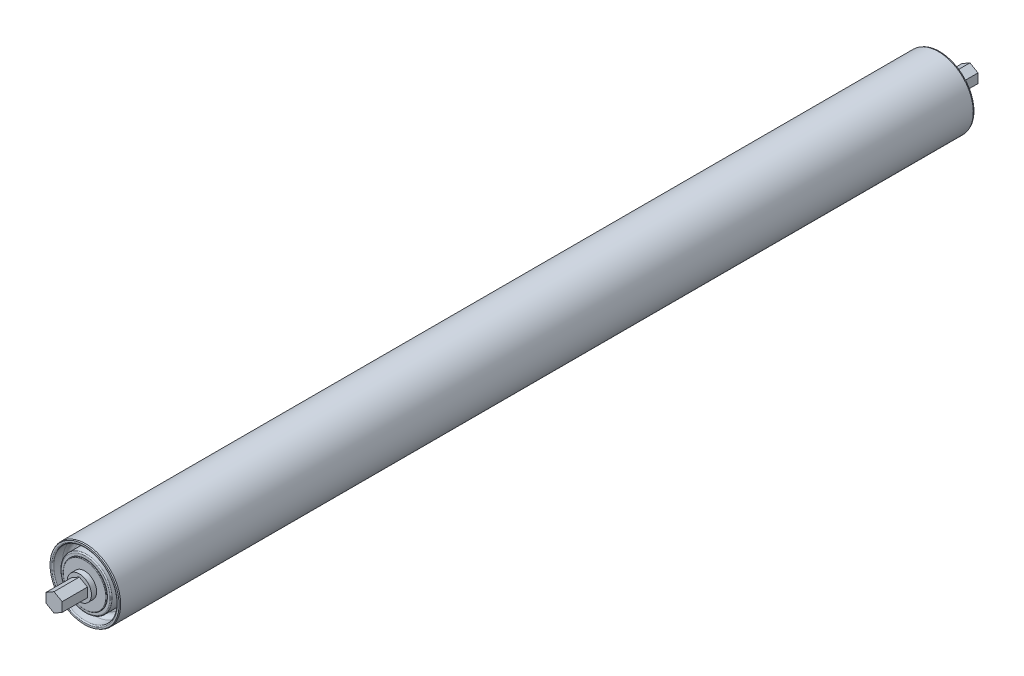
SolidWorks part; units mm, degrees
ref_plane "Front Plane" through (0, 0, 0) normal (0, 0, 1) x (1, 0, 0)
ref_plane "Top Plane" through (0, 0, 0) normal (0, 1, 0) x (1, 0, 0)
ref_plane "Right Plane" through (0, 0, 0) normal (1, 0, 0) x (0, 0, -1)
sketch "Sketch1" plane through (0, 0, 0) normal (1, 0, 0) x (0, 0, -1)
  line L0 (-315.9125, 0) -> (315.9125, 0) construction
  line L1 (-294.0844, 24.13) -> (294.0844, 24.13)
  line L2 (0, 24.13) -> (0, 0) construction
  line L3 (-315.9125, 0) -> (-315.9125, 5.5562)
  line L4 (-315.9125, 5.5562) -> (-294.0844, 5.5562)
  line L5 (-300.0375, 5.5562) -> (-300.0375, -5.5562) construction
  line L6 (300.0375, 5.5562) -> (300.0375, -5.5562) construction
  line L7 (-300.0375, -5.5562) -> (300.0375, -5.5562) construction
  line L8 (-294.0844, 24.13) -> (-294.0844, 0) construction
  line L9 (-298.45, 8.3344) -> (-298.45, 0)
  line L10 (-298.45, 8.3344) -> (-294.0844, 8.3344)
  line L11 (298.45, 8.3344) -> (294.0844, 8.3344)
  line L12 (298.45, 8.3344) -> (298.45, 0)
  line L13 (315.9125, 5.5563) -> (294.0844, 5.5563)
  line L14 (315.9125, 0) -> (315.9125, 5.5563)
  line L15 (-294.8781, 15.0019) -> (-294.1161, 15.0019) construction
  line L16 (-294.0844, 24.13) -> (-294.8781, 23.8125)
  line L17 (-294.8781, 23.8125) -> (-294.8781, 8.3344)
  line L18 (294.0844, 24.13) -> (294.8781, 23.8125)
  line L19 (294.8781, 23.8125) -> (294.8781, 8.3344)
  line L20 (-294.1161, 15.0019) -> (-294.1161, 17.5022) construction
  line L22 (-294.1161, 17.5022) -> (-284.9563, 17.5022) construction
  line L23 (-284.9563, 17.5022) -> (-284.9563, 21.971) construction
  line L24 (-284.9563, 21.971) -> (-294.8781, 21.971) construction
  arc A1 (-288.0043, 21.971) -> (-284.9563, 18.923) centre (-288.0043, 18.923) cw construction
  arc A2 (-294.8781, 22.733) -> (-294.1161, 21.971) centre (-294.1161, 22.733) ccw construction
  arc A3 (-294.1161, 16.7402) -> (-293.3541, 17.5022) centre (-293.3541, 16.7402) cw construction
  arc A4 (-294.8781, 14.6209) -> (-294.4971, 15.0019) centre (-294.4971, 14.6209) cw construction
  point P11 (-300.0375, 0)
  point P12 (300.0375, 0)
  point P13 (0, -5.5562)
  point P24 (-270.1925, 0)
  point P27 (270.1925, 0)
  point P32 (-284.9563, 19.7366)
  dimension "D14" = 3.048
  dimension "D15" = 0.762
  dimension "D16" = 0.381
  dimension "Overall Width" = 631.825
  dimension "Rollar Diameter" = 48.26
  dimension "Hex Axle Size" = 11.1125
  dimension "BF" = 600.075
  dimension "D2" = 16.6687
  dimension "D1" = 1.5875
  dimension "D5" = 15.875
  dimension "D6" = 45.72
  dimension "D7" = 45.72
  dimension "D3" = 4.3656
  dimension "D8" = 47.625
  dimension "D10" = 0.762
  dimension "D9" = 35.0044
  dimension "D11" = 30.0038
  dimension "D12" = 43.942
  dimension "D13" = 13.4937
  dimension "Rollar Width" = 589.7563
sketch "Sketch5" plane through (0, 0, 0) normal (0, 0, 1) x (1, 0, 0)
  circle A0 centre (0, 0) radius 24.13
  dimension "D1" = 48.26
sketch "Sketch3" plane through (0, 0, 0) normal (1, 0, 0) x (0, 0, -1)
  line L0 (315.9125, 5.5563) -> (294.0844, 5.5563) construction
  line L1 (315.9125, 0) -> (315.9125, 5.5563) construction
  line L2 (-315.9125, 0) -> (-315.9125, 5.5562) construction
  line L3 (-315.9125, 5.5562) -> (-294.0844, 5.5562) construction
  line L4 (294.8781, 23.8125) -> (294.8781, 8.3344) construction
  line L5 (294.0844, 24.13) -> (294.8781, 23.8125) construction
  line L6 (-294.0844, 24.13) -> (294.0844, 24.13) construction
  line L7 (-294.0844, 24.13) -> (-294.8781, 23.8125) construction
  line L8 (-294.8781, 23.8125) -> (-294.8781, 8.3344) construction
  line L9 (298.45, 8.3344) -> (294.0844, 8.3344) construction
  line L10 (298.45, 8.3344) -> (298.45, 0) construction
  line L11 (-298.45, 8.3344) -> (-298.45, 0) construction
  line L12 (-298.45, 8.3344) -> (-294.0844, 8.3344) construction
  line L13 (315.9125, 5.5563) -> (298.45, 5.5563)
  line L14 (315.9125, 0) -> (315.9125, 5.5563)
  line L15 (-315.9125, 0) -> (-315.9125, 5.5562)
  line L16 (-315.9125, 5.5562) -> (-298.45, 5.5562)
  line L17 (294.8781, 23.8125) -> (294.8781, 8.3344)
  line L18 (294.0844, 24.13) -> (294.8781, 23.8125)
  line L19 (-294.0844, 24.13) -> (294.0844, 24.13)
  line L20 (-294.0844, 24.13) -> (-294.8781, 23.8125)
  line L21 (-294.8781, 23.8125) -> (-294.8781, 8.3344)
  line L22 (298.45, 8.3344) -> (294.8781, 8.3344)
  line L23 (298.45, 8.3344) -> (298.45, 5.5563)
  line L24 (-298.45, 8.3344) -> (-298.45, 5.5562)
  line L25 (-298.45, 8.3344) -> (-294.8781, 8.3344)
  line L26 (-315.9125, 0) -> (315.9125, 0)
revolve "Revolve1" add sketch "Sketch3" angle 360 about L0
sketch "Sketch4" plane through (0, 0, 315.9125) normal (0, 0, 1) x (1, 0, 0)
  line L1 (0, 6.4158) -> (-5.5562, 3.2079)
  line L2 (-5.5562, 3.2079) -> (-5.5562, -3.2079)
  line L3 (-5.5562, -3.2079) -> (0, -6.4158)
  line L4 (0, -6.4158) -> (5.5562, -3.2079)
  line L5 (5.5562, -3.2079) -> (5.5562, 3.2079)
  line L6 (5.5562, 3.2079) -> (0, 6.4158)
  circle A0 centre (0, 0) radius 5.5562 construction
extrude "Boss-Extrude1" add sketch "Sketch4" against normal up to surface (631.825 mm away) up to face at (0, -5.5562, -315.9125)
sketch "Sketch6" plane through (0, 0, 0) normal (1, 0, 0) x (0, 0, -1)
  line L0 (-284.9563, 21.971) -> (-294.8781, 21.971) construction
  line L1 (-284.9563, 17.5022) -> (-284.9563, 21.971) construction
  line L2 (-294.1161, 17.5022) -> (-284.9563, 17.5022) construction
  line L3 (-294.1161, 15.0019) -> (-294.1161, 17.5022) construction
  line L4 (-294.8781, 15.0019) -> (-294.1161, 15.0019) construction
  line L5 (-288.0043, 21.971) -> (-294.1161, 21.971)
  line L6 (-284.9563, 17.5022) -> (-284.9563, 18.923)
  line L7 (-293.3541, 17.5022) -> (-284.9563, 17.5022)
  line L8 (-294.1161, 15.0019) -> (-294.1161, 16.7402)
  line L9 (-294.4971, 15.0019) -> (-294.1161, 15.0019)
  line L10 (-294.8781, 22.733) -> (-294.8781, 14.6209)
  arc A0 (-294.8781, 22.733) -> (-294.1161, 21.971) centre (-294.1161, 22.733) ccw construction
  arc A1 (-284.9563, 18.923) -> (-288.0043, 21.971) centre (-288.0043, 18.923) ccw construction
  arc A2 (-293.3541, 17.5022) -> (-294.1161, 16.7402) centre (-293.3541, 16.7402) ccw construction
  arc A3 (-294.4971, 15.0019) -> (-294.8781, 14.6209) centre (-294.4971, 14.6209) ccw construction
  arc A4 (-294.8781, 22.733) -> (-294.1161, 21.971) centre (-294.1161, 22.733) ccw
  arc A5 (-284.9563, 18.923) -> (-288.0043, 21.971) centre (-288.0043, 18.923) ccw
  arc A6 (-293.3541, 17.5022) -> (-294.1161, 16.7402) centre (-293.3541, 16.7402) ccw
  arc A7 (-294.4971, 15.0019) -> (-294.8781, 14.6209) centre (-294.4971, 14.6209) ccw
revolve "Cut-Revolve1" cut sketch "Sketch6" angle 360 about L0
mirror "Mirror2" about plane through (0, 0, 0) normal (0, 0, 1) of "Cut-Revolve1"
ref_plane "Contact Plane 1" through (0, 24.13, 0) normal (0, 1, 0) x (1, 0, 0)
equation "\"D2@Sketch1\"=\"Hex Axle Size@Sketch1\"*1.5"
equation "\"D7@Sketch1\"=\"D6@Sketch1\""
equation "\"D9@Sketch1\"=\"D2@Sketch1\"*2.1"
equation "\"D11@Sketch1\"=\"D2@Sketch1\"*1.8"
equation "\"D12@Sketch1\"=1.7+\"D10@Sketch1\""
equation "\"D16@Sketch1\"=\"D15@Sketch1\"/2"
